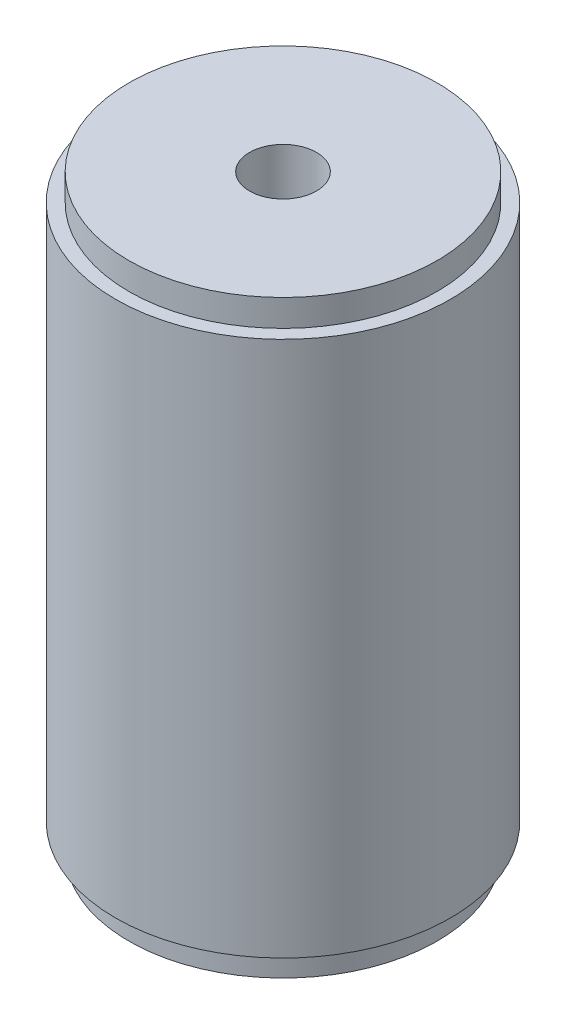
SolidWorks part; units mm, degrees
ref_plane "Front Plane" through (0, 0, 0) normal (0, 0, 1) x (1, 0, 0)
ref_plane "Top Plane" through (0, 0, 0) normal (0, 1, 0) x (1, 0, 0)
ref_plane "Right Plane" through (0, 0, 0) normal (1, 0, 0) x (0, 0, -1)
sketch "Sketch1" plane through (0, 0, 0) normal (0, 1, 0) x (1, 0, 0)
  circle A0 centre (0, 0) radius 12.5
  dimension "D1" = 25
extrude "Boss-Extrude1" add sketch "Sketch1" along normal blind 40
sketch "Sketch2" plane through (0, 40, 0) normal (0, 1, 0) x (1, 0, 0)
  circle A0 centre (0, 0) radius 11.5
  dimension "D1" = 23
extrude "Boss-Extrude2" add sketch "Sketch2" along normal blind 2
sketch "Sketch3" plane through (0, 0, 0) normal (0, -1, 0) x (1, 0, 0)
  circle A0 centre (0, 0) radius 11.5
  dimension "D1" = 23
extrude "Boss-Extrude3" add sketch "Sketch3" along normal blind 2
sketch "Sketch4" plane through (0, -2, 0) normal (0, -1, 0) x (-1, 0, 0)
  circle A0 centre (0, 0) radius 2.5
  dimension "D1" = 5
extrude "Cut-Extrude1" cut sketch "Sketch4" against normal through all both and the other way through all
